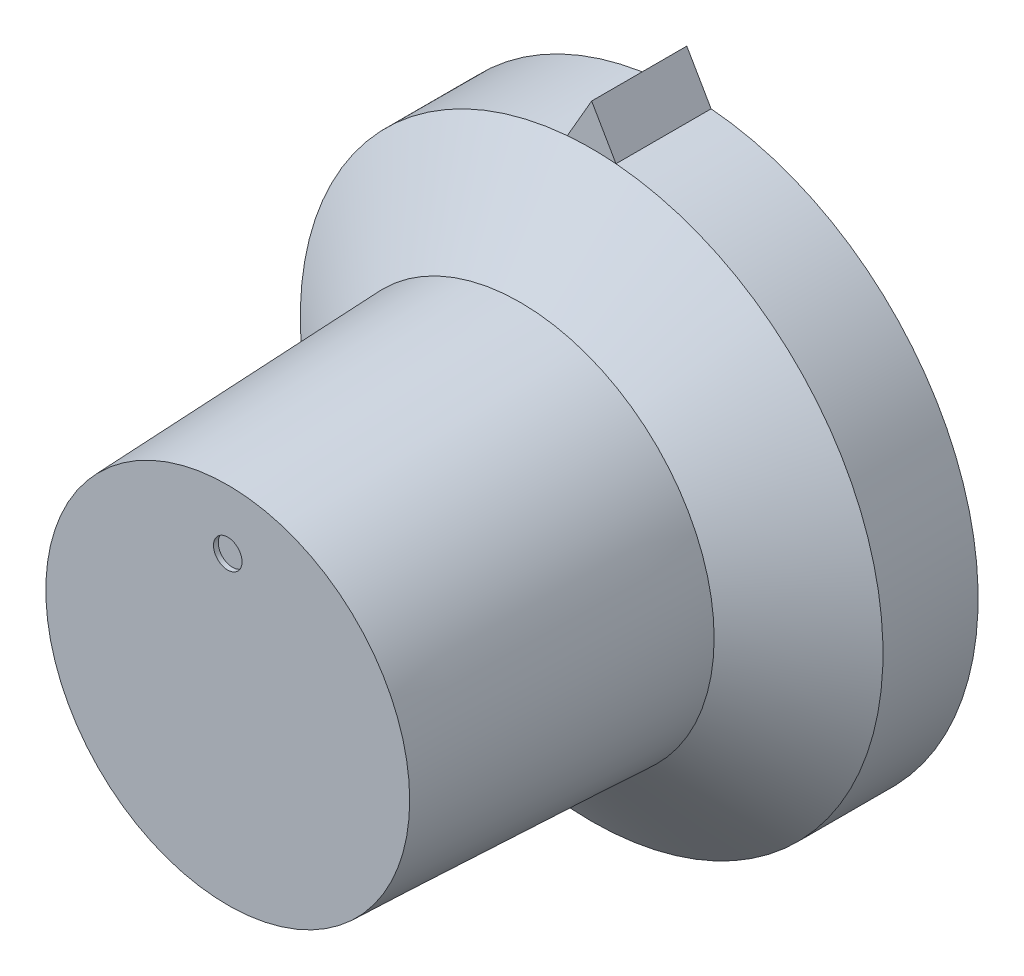
SolidWorks part; units mm, degrees
ref_plane "Front Plane" through (0, 0, 0) normal (0, 0, 1) x (1, 0, 0)
ref_plane "Top Plane" through (0, 0, 0) normal (0, 1, 0) x (1, 0, 0)
ref_plane "Right Plane" through (0, 0, 0) normal (1, 0, 0) x (0, 0, -1)
sketch "Sketch2" plane through (0, 0, 0) normal (1, 0, 0) x (0, 0, -1)
  line L0 (0, 7.65) -> (0, -7.65)
  line L1 (0, 0) -> (24.6, 0) construction
  line L2 (12.3, -8.15) -> (12.3, 8.15)
  line L3 (0, 7.65) -> (12.3, 8.15)
  line L4 (0, -7.65) -> (12.3, -8.15)
  line L5 (15.3, 12.25) -> (15.3, -12.25)
  line L6 (12.3, 8.15) -> (15.3, 12.25)
  line L7 (12.3, -8.15) -> (15.3, -12.25)
  line L8 (19.3, 12.25) -> (19.3, -12.25)
  line L9 (15.3, 12.25) -> (19.3, 12.25)
  line L10 (15.3, -12.25) -> (19.3, -12.25)
  point P6 (12.3, 0)
  point P7 (15.3, 0)
  point P8 (19.3, 0)
  dimension "D1" = 15.3
  dimension "D2" = 16.3
  dimension "D3" = 12.3
  dimension "D4" = 24.5
  dimension "D5" = 3
  dimension "D6" = 24.5
  dimension "D7" = 4
revolve "Revolve3" add sketch "Sketch2" angle 360 about L1
sketch "Sketch3" plane through (0, 0, -19.3) normal (0, 0, -1) x (-1, 0, 0)
  line L0 (0, 0) -> (0, 12.25) construction
  line L1 (0, 12.25) -> (0, 13.98) construction
  line L2 (0, 13.98) -> (1.1547, 11.98)
  line L3 (0, 13.98) -> (-1.1547, 11.98)
  line L4 (1.1547, 11.98) -> (-1.1547, 11.98)
  circle A0 centre (0, 0) radius 12.25 construction
  dimension "D1" = 1.73
  dimension "D2" = 30
  dimension "D3" = 2
extrude "Boss-Extrude1" add sketch "Sketch3" against normal blind 4
sketch "Sketch4" plane through (0, 0, 0) normal (0, 0, 1) x (1, 0, 0)
  line L0 (0, 0) -> (0, 7.65) construction
  line L1 (0, 7.65) -> (0, 5.15) construction
  circle A0 centre (0, 0) radius 7.65 construction
  circle A1 centre (0, 5.15) radius 0.6
  dimension "D2" = 1.2
  dimension "D1" = 2.5
extrude "Cut-Extrude1" cut sketch "Sketch4" against normal blind 0.2
sketch "Sketch5" plane through (0, 0, -19.3) normal (0, 0, -1) x (-1, 0, 0)
  circle A0 centre (0, 0) radius 11
  dimension "D1" = 22
extrude "Cut-Extrude2" cut sketch "Sketch5" against normal blind 4
sketch "Sketch6" plane through (0, 0, -15.3) normal (0, 0, -1) x (-1, 0, 0)
  circle A0 centre (0, 0) radius 3
  dimension "D1" = 6
extrude "Cut-Extrude3" cut sketch "Sketch6" against normal blind 11
